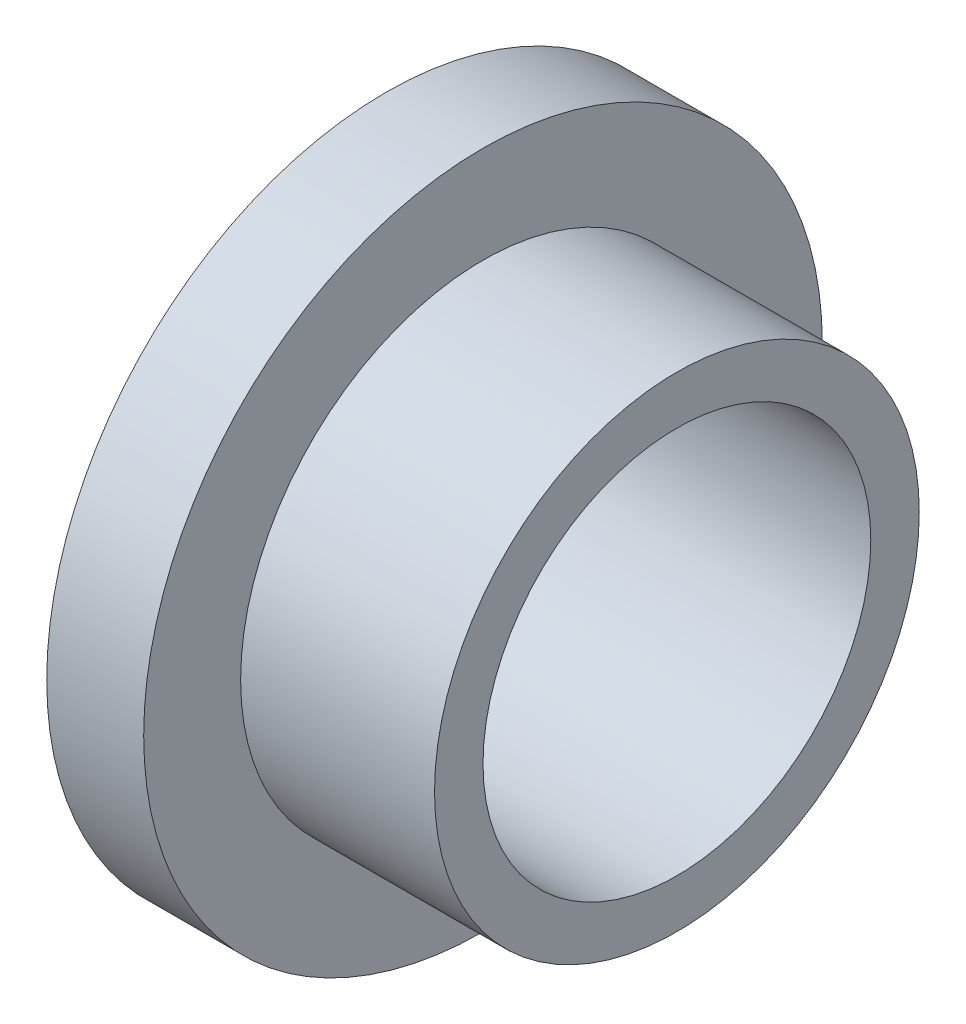
SolidWorks part; units mm, degrees
material "Commercial Bronze, UNS C22000 (90-10 Bronze)"
ref_plane "Front Plane" through (0, 0, 0) normal (0, 0, 1) x (1, 0, 0)
ref_plane "Top Plane" through (0, 0, 0) normal (0, 1, 0) x (1, 0, 0)
ref_plane "Right Plane" through (0, 0, 0) normal (1, 0, 0) x (0, 0, -1)
sketch "Sketch1" plane through (0, 0, 0) normal (1, 0, 0) x (0, 0, -1)
  circle A0 centre (0, 0) radius 6.35
  circle A1 centre (0, 0) radius 7.9375
extrude "Boss-Extrude1" add sketch "Sketch1" along normal blind 9.525
sketch "Sketch2" plane through (0, 0, 0) normal (-1, 0, 0) x (0, 0, 1)
  circle A0 centre (0, 0) radius 11.1125
  circle A1 centre (0, 0) radius 6.35
extrude "Boss-Extrude2" add sketch "Sketch2" against normal blind 3.175
